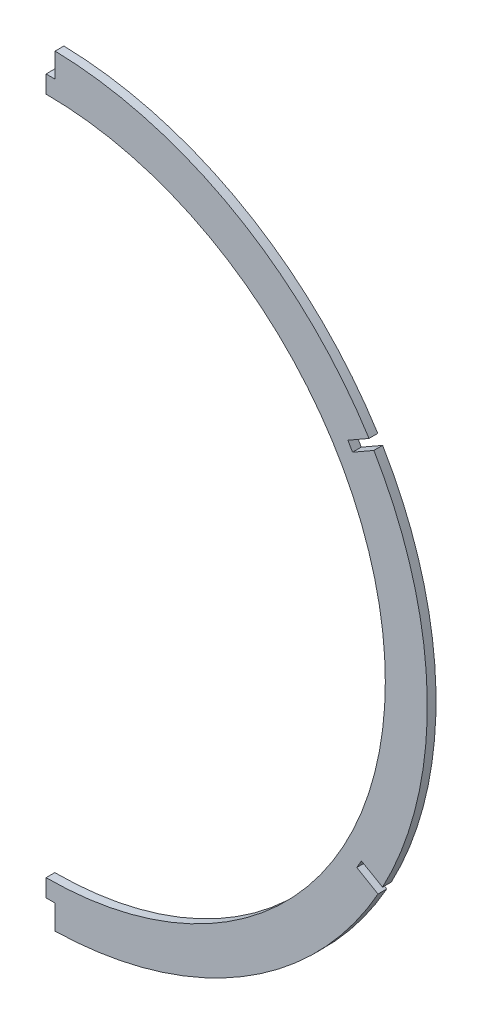
SolidWorks part; units mm, degrees
material "Plywood"
ref_plane "Front Plane" through (0, 0, 0) normal (0, 0, 1) x (1, 0, 0)
ref_plane "Top Plane" through (0, 0, 0) normal (0, 1, 0) x (1, 0, 0)
ref_plane "Right Plane" through (0, 0, 0) normal (1, 0, 0) x (0, 0, -1)
sketch "Sketch1" plane through (0, 0, 0) normal (0, 0, 1) x (1, 0, 0)
  line L0 (0, 32.094) -> (0, -346.2619) construction
  line L1 (0, 0) -> (0, 244.345) construction
  line L2 (0, 0) -> (0, 471.6969) construction
  line L3 (0, 0) -> (-283.5939, 0) construction
  line L4 (-127.2933, -32.5553) -> (-85.9841, -73.8644)
  line L5 (-85.9841, -73.8644) -> (-85.9841, -86.6438)
  line L6 (-85.9841, -73.8644) -> (-54.3993, -105.4493) construction
  arc A0 (-54.3993, -105.4493) -> (-127.2933, -32.5553) centre (0, 21.844) ccw
  arc A2 (-82.075, -89.6305) -> (-54.3993, -105.4493) centre (0, 21.844) ccw construction
  arc A3 (-127.2933, -32.5553) -> (-82.075, -89.6305) centre (0, 21.844) ccw construction
  arc A4 (-85.9841, -86.6438) -> (-54.3993, -105.4493) centre (0, 21.844) ccw
  spline S2 degree 3 poles (-19.218, -1838.2141) (276.9397, -392.4777) (232.9593, 72.7514) (49.9381, 150.9258) (45.7097, 152.4909) (37.1079, 155.2035) (32.7346, 156.3511) (27.1752, 157.5183) (26.0587, 157.7384) (23.8163, 158.1514) (22.6888, 158.3447) (19.306, 158.8811) (17.0511, 159.1813) (10.2867, 159.9126) (1.2693, 160.4377) (-7.745, 160.0789) (-14.5046, 159.4749) (-16.7575, 159.2176) (-20.1367, 158.7464) (-21.263, 158.5751) (-23.5156, 158.2037) (-24.6421, 158.0036) (-30.2426, 156.9366) (-34.6466, 155.8674) (-43.3063, 153.3113) (-47.562, 151.8242) (-55.9254, 148.4331) (-60.0331, 146.529) (-66.0807, 143.3516) (-68.0818, 142.2359) (-72.0044, 139.9197) (-73.9301, 138.7173) (-79.6017, 134.9792) (-86.884, 129.6473) (-93.6143, 123.6295) (-98.4521, 118.8554) (-100.0296, 117.2204) (-102.3424, 114.7015) (-103.1054, 113.8496) (-104.6077, 112.1297) (-105.3467, 111.2623) (-108.9818, 106.8875) (-111.6981, 103.2683) (-116.7574, 95.7975) (-119.1004, 91.9459) (-123.4121, 84.0098) (-125.3809, 79.9253) (-127.6006, 74.6695) (-128.0327, 73.61) (-128.8681, 71.4874) (-129.2719, 70.423) (-130.4422, 67.2205) (-131.1674, 65.0732) (-133.1812, 58.5951) (-135.4347, 49.861) (-136.834, 40.9354) (-137.5569, 34.168) (-137.7434, 31.9) (-137.9397, 28.4793) (-137.9911, 27.3374) (-138.0656, 25.0596) (-138.0887, 23.9223) (-138.135, 18.2442) (-137.9496, 13.7276) (-137.1441, 4.7454) (-136.5239, 0.2797) (-134.8456, -8.6005) (-133.7876, -13.015) (-131.2181, -21.791) (-129.7278, -26.0794) (-126.351, -34.4622) (-124.4643, -38.5569) (-120.2966, -46.5538) (-118.0156, -50.456) (-114.9122, -55.2108) (-114.2789, -56.1556) (-112.9868, -58.0327) (-112.3272, -58.9661) (-110.315, -61.7398) (-108.9333, -63.5482) (-104.6702, -68.8537) (-98.6716, -75.6089) (-92.0553, -81.7381) (-86.8592, -86.0978) (-85.0881, -87.5114) (-82.3719, -89.5716) (-81.4566, -90.2482) (-79.6058, -91.5811) (-78.6696, -92.238) (117.1329, -226.0075) (630.1685, 154.3992) (1500.4507, 1111.3958) knots -1.313799 -1.313799 -1.313799 -1.313799 0.03125 0.03125 0.0625 0.0625 0.09375 0.09375 0.101563 0.101563 0.109375 0.109375 0.125 0.125 0.15625 0.1875 0.1875 0.203125 0.203125 0.210937 0.210937 0.21875 0.21875 0.25 0.25 0.28125 0.28125 0.3125 0.3125 0.328125 0.328125 0.34375 0.34375 0.375 0.40625 0.40625 0.421875 0.421875 0.429687 0.429687 0.4375 0.4375 0.46875 0.46875 0.5 0.5 0.53125 0.53125 0.539062 0.539062 0.546875 0.546875 0.5625 0.5625 0.59375 0.625 0.625 0.640625 0.640625 0.648437 0.648437 0.65625 0.65625 0.6875 0.6875 0.71875 0.71875 0.75 0.75 0.78125 0.78125 0.8125 0.8125 0.84375 0.84375 0.851562 0.851562 0.859375 0.859375 0.875 0.875 0.90625 0.9375 0.9375 0.953125 0.953125 0.960937 0.960937 0.96875 0.96875 2.582348 2.582348 2.582348 2.582348 only from (66.3397, 143.1887) to (-66.0465, -100.0388)
  spline S3 degree 3 poles (66.3397, 143.1887) (62.3323, 145.3909) (58.2494, 147.3758) (49.9381, 150.9258) (45.7097, 152.4909) (37.1079, 155.2035) (32.7346, 156.3511) (27.1752, 157.5183) (26.0587, 157.7384) (23.8163, 158.1514) (22.6888, 158.3447) (19.306, 158.8811) (17.0511, 159.1813) (10.2867, 159.9126) (1.2693, 160.4377) (-7.745, 160.0789) (-14.5046, 159.4749) (-16.7575, 159.2176) (-20.1367, 158.7464) (-21.263, 158.5751) (-23.5156, 158.2037) (-24.6421, 158.0036) (-30.2426, 156.9366) (-34.6466, 155.8674) (-43.3063, 153.3113) (-47.562, 151.8242) (-55.9254, 148.4331) (-60.0331, 146.529) (-66.0807, 143.3516) (-68.0818, 142.2359) (-72.0044, 139.9197) (-73.9301, 138.7173) (-79.6017, 134.9792) (-86.884, 129.6473) (-93.6143, 123.6295) (-98.4521, 118.8554) (-100.0296, 117.2204) (-102.3424, 114.7015) (-103.1054, 113.8496) (-104.6077, 112.1297) (-105.3467, 111.2623) (-108.9818, 106.8875) (-111.6981, 103.2683) (-116.7574, 95.7975) (-119.1004, 91.9459) (-123.4121, 84.0098) (-125.3809, 79.9253) (-127.6006, 74.6695) (-128.0327, 73.61) (-128.8681, 71.4874) (-129.2719, 70.423) (-130.4422, 67.2205) (-131.1674, 65.0732) (-133.1812, 58.5951) (-135.4347, 49.861) (-136.834, 40.9354) (-137.5569, 34.168) (-137.7434, 31.9) (-137.9397, 28.4793) (-137.9911, 27.3374) (-138.0656, 25.0596) (-138.0887, 23.9223) (-138.135, 18.2442) (-137.9496, 13.7276) (-137.1441, 4.7454) (-136.5239, 0.2797) (-134.8456, -8.6005) (-133.7876, -13.015) (-131.2181, -21.791) (-129.7278, -26.0794) (-127.6847, -31.1513) (-127.3213, -32.0275) (-126.9491, -32.8995) knots 0 0 0 0 0.03125 0.03125 0.0625 0.0625 0.09375 0.09375 0.101563 0.101563 0.109375 0.109375 0.125 0.125 0.15625 0.1875 0.1875 0.203125 0.203125 0.210937 0.210937 0.21875 0.21875 0.25 0.25 0.28125 0.28125 0.3125 0.3125 0.328125 0.328125 0.34375 0.34375 0.375 0.40625 0.40625 0.421875 0.421875 0.429687 0.429687 0.4375 0.4375 0.46875 0.46875 0.5 0.5 0.53125 0.53125 0.539062 0.539062 0.546875 0.546875 0.5625 0.5625 0.59375 0.625 0.625 0.640625 0.640625 0.648437 0.648437 0.65625 0.65625 0.6875 0.6875 0.71875 0.71875 0.75 0.75 0.78125 0.78125 0.787815 0.787815 0.787815 0.787815 construction
  point P2 (0, 160.2226)
  point P3 (0, -116.9127)
  point P23 (-85.9841, -73.8644)
  dimension "D1" = 277.1353
  dimension "D2" = 276.86
  dimension "D3" = 21.844
  dimension "D5" = 45
  dimension "D6" = 113.03
  dimension "D4" = 58.42
  dimension "D7" = 45
extrude "Boss-Extrude1" add sketch "Sketch1" along normal mid plane 3.175
sketch "Sketch2" plane through (0, 0, 1.5875) normal (0, 0, 1) x (1, 0, 0)
  line L4 (-114.3729, -23.9231) -> (-70.7441, -67.5518)
  line L5 (-70.7441, -67.5518) -> (-70.7441, -79.0076)
  line L6 (-114.3729, -23.9231) -> (-70.7441, -67.5518)
  line L7 (-70.7441, -67.5518) -> (-70.7441, -79.0076)
  arc A2 (-70.7441, -79.0076) -> (-114.3729, -23.9231) centre (0, 21.844) ccw
  arc A3 (-70.7441, -79.0076) -> (-114.3729, -23.9231) centre (0, 21.844) ccw
  dimension "D1" = 15.24
extrude "Cut-Extrude1" cut sketch "Sketch2" against normal up to surface (3.175 mm away) up to face at (-27.5361, -9.1994, -1.5875)
fillet "Fillet1" radius 8.89 6 edges at (-127.2933, -32.5553, 0) (-114.3729, -23.9231, 0) (-85.9841, -73.8644, 0) (-85.9841, -86.6438, 0) (-70.7441, -67.5518, 0) (-70.7441, -79.0076, 0)
sketch "Sketch3" plane through (0, 0, 1.5875) normal (0, 0, 1) x (1, 0, 0)
  line L0 (0, 49.992) -> (0, 733.2) construction
  line L1 (0, 49.992) -> (0, 733.2) construction
  line L2 (-136.2041, -28.3557) -> (0, 49.992) construction
  line L3 (136.2041, -28.3557) -> (0, 49.992) construction
  line L4 (-136.2041, -28.3557) -> (0, 49.992) construction
  line L5 (136.2041, -28.3557) -> (0, 49.992) construction
  line L6 (-1.651, 152.6442) -> (-1.651, 160.2642)
  line L7 (1.651, 152.6442) -> (1.651, 160.2642)
  line L8 (-1.651, 152.6442) -> (1.651, 152.6442)
  line L9 (119.8454, -45.9681) -> (106.751, -38.3801)
  line L10 (121.4405, -43.2127) -> (108.3453, -35.6242)
  line L11 (-126.0584, -33.7901) -> (-88.588, -71.2606)
  line L12 (-85.9841, -77.5468) -> (-85.9841, -82.2574)
  line L13 (-126.0584, -33.7901) -> (-88.588, -71.2606) construction
  line L14 (-85.9841, -77.5468) -> (-85.9841, -82.2574) construction
  line L18 (121.4405, -43.2127) -> (108.3453, -35.6242)
  line L30 (-123.167, -47.8929) -> (-104.8699, -37.29)
  line L35 (119.8454, -45.9681) -> (106.751, -38.3801)
  line L36 (-109.2131, -37.6397) -> (-109.8693, -36.5073)
  line L47 (108.5244, -35.721) -> (120.1169, -46.1175) construction
  line L48 (114.3206, -40.9193) -> (126.5619, -48.0121) construction
  line L49 (113.8577, -42.5592) -> (122.0137, -47.2849)
  line L50 (115.5132, -39.7021) -> (123.6691, -44.4278)
  line L51 (113.8577, -42.5592) -> (115.5132, -39.7021)
  line L52 (122.0137, -47.2849) -> (123.6691, -44.4278)
  line L58 (-124.7703, -45.1423) -> (-109.8693, -36.5073)
  line L59 (-124.7703, -45.1423) -> (-123.167, -47.8929)
  line L67 (-105.8098, -35.6675) -> (-109.2131, -37.6397)
  line L71 (-124.7703, -45.1423) -> (-123.167, -47.8929) construction
  line L72 (-124.7703, -45.1423) -> (-109.8693, -36.5073) construction
  line L73 (-123.167, -47.8929) -> (-104.8699, -37.29) construction
  line L74 (-123.167, -47.8929) -> (-107.9499, -35.3951) construction
  line L75 (-115.5584, -41.644) -> (-110.9064, -38.9482) construction
  line L76 (-119.3826, -41.9518) -> (-112.6266, -38.0369)
  line L77 (-117.727, -44.8088) -> (-110.971, -40.8938)
  line L78 (-119.3826, -41.9518) -> (-117.727, -44.8088)
  line L79 (-112.6266, -38.0369) -> (-110.971, -40.8938)
  line L82 (-105.8098, -35.6675) -> (-109.2131, -37.6397) construction
  line L83 (-109.2131, -37.6397) -> (-109.8693, -36.5073) construction
  arc A0 (-54.3993, -105.4493) -> (-127.2933, -32.5553) centre (0, 21.844) ccw construction
  arc A2 (-1.651, 160.2642) -> (-130.2816, -24.9489) centre (0, 21.844) ccw construction
  arc A3 (-130.2816, -24.9489) -> (-127.2933, -32.5553) centre (0, 21.844) ccw construction
  arc A4 (-1.651, 160.2642) -> (-130.2816, -24.9489) centre (0, 21.844) ccw construction
  arc A5 (-130.2816, -24.9489) -> (-127.9919, -30.8906) centre (0, 21.844) ccw construction
  arc A6 (-82.3849, -89.4016) -> (-127.9919, -30.8906) centre (0, 21.844) ccw
  arc A7 (-127.9919, -30.8906) -> (-126.0584, -33.7901) centre (-119.7722, -27.504) ccw
  arc A8 (-85.9841, -77.5468) -> (-88.588, -71.2606) centre (-94.8741, -77.5468) ccw
  arc A9 (-85.9841, -82.2574) -> (-82.3849, -89.4016) centre (-77.0941, -82.2574) ccw
  arc A11 (-127.9919, -30.8906) -> (-126.0584, -33.7901) centre (-119.7722, -27.504) ccw construction
  arc A12 (-85.9841, -77.5468) -> (-88.588, -71.2606) centre (-94.8741, -77.5468) ccw construction
  arc A13 (-85.9841, -82.2574) -> (-82.3849, -89.4016) centre (-77.0941, -82.2574) ccw construction
  arc A14 (130.2816, -24.9489) -> (1.651, 160.2642) centre (0, 21.844) ccw construction
  arc A15 (1.651, 160.2642) -> (-1.651, 160.2642) centre (0, 21.844) ccw
  arc A16 (130.2816, -24.9489) -> (1.651, 160.2642) centre (0, 21.844) ccw construction
  arc A17 (1.651, 160.2642) -> (-1.651, 160.2642) centre (0, 21.844) ccw
  spline S0 degree 3 poles (106.751, -38.3801) (107.2824, -37.4615) (107.8139, -36.5429) (108.3453, -35.6242) knots 0 0 0 0 1 1 1 1 weights 1 1 1 1
  spline S1 degree 3 poles (119.8454, -45.9681) (120.3771, -45.0496) (120.9088, -44.1312) (121.4405, -43.2127) knots 0 0 0 0 1 1 1 1 weights 1 1 1 1
  spline S2 degree 3 poles (-885.9995, -1769.7517) (-211.5636, -622.9991) (457.4593, 532.6423) (1115.3786, 1687.3419) knots -628.025775 -628.025775 -628.025775 -628.025775 629.321979 629.321979 629.321979 629.321979 weights 1.00213 0.999289 0.99929 1.002132 only from (119.8454, -45.9681) to (121.4405, -43.2127)
  spline S3 degree 3 poles (-1102.3122, 1695.2927) (-441.4553, 540.1286) (227.4994, -614.6331) (901.0143, -1762.8764) knots -1066.678373 -1066.678373 -1066.678373 -1066.678373 1067.563855 1067.563855 1067.563855 1067.563855 weights 1.001327 0.999558 0.999558 1.001327 only from (-105.8098, -35.6675) to (-104.8699, -37.29)
  spline S4 degree 3 poles (-105.8098, -35.6675) (-105.4965, -36.2084) (-105.1832, -36.7492) (-104.8699, -37.29) knots 0 0 0 0 1 1 1 1 weights 1 1 1 1 construction
  spline S6 degree 3 poles (-898.4881, -1762.9922) (-224.3422, -615.0331) (444.2887, 540.7283) (1102.2727, 1695.4213) knots -627.922306 -627.922306 -627.922306 -627.922306 629.42597 629.42597 629.42597 629.42597 weights 1.001921 0.999359 0.99936 1.001924 only from (106.751, -38.3801) to (108.3453, -35.6242)
  point P49 (-116.0256, -43.8229)
  point P50 (120.451, -46.3794)
  arc M19 (-82.3849, -89.4016) -> (-127.9919, -30.8906) centre (0, 21.844) ccw
  line M21 (-126.0584, -33.7901) -> (-88.588, -71.2606)
  dimension "D1" = 3.302
  dimension "D2" = 7.62
  dimension "D4" = 3.302
  dimension "D5" = 7.62
  dimension "D6" = 3.302
  dimension "D7" = 5.842
  dimension "D3" = 0
extrude "Cut-Extrude2" [suppressed] cut sketch "Sketch3" against normal through all contours L79 L76 L77 M21 | L6 L8 L7 M19 | L51 L49 L50 M19
sketch "Sketch4" plane through (0, 0, 0) normal (1, 0, 0) x (0, 0, -1)
  line L1 (-96.2805, 232.7957) -> (122.2438, 232.7957)
  line L2 (-96.2805, 232.7957) -> (-96.2805, -207.8589)
  line L3 (-96.2805, -207.8589) -> (122.2438, -207.8589)
  line L4 (122.2438, 232.7957) -> (122.2438, -207.8589)
extrude "Cut-Extrude3" cut sketch "Sketch4" against normal through all
sketch "Sketch5" plane through (0, 0, -1.5875) normal (0, 0, -1) x (-1, 0, 0)
  line L0 (0, 0) -> (0, 145.034) construction
  line L1 (0, 145.034) -> (0, 151.384) construction
  line L2 (104.929, 86.3862) -> (0, 26.2525) construction
  line L3 (-3.302, 151.384) -> (3.302, 151.384)
  line L4 (0, 151.384) -> (0, 164.084)
  line L5 (-3.302, 164.084) -> (3.302, 164.084)
  line L6 (3.302, 151.384) -> (3.302, 164.084)
  line L7 (104.929, 86.3862) -> (110.4384, 89.5435) construction
  line L8 (109.5985, 91.009) -> (111.2782, 88.078)
  line L9 (109.5985, 91.009) -> (120.6173, 97.3238)
  line L10 (111.2782, 88.078) -> (122.297, 94.3928)
  line L11 (120.6173, 97.3238) -> (122.297, 94.3928)
  line L12 (108.1767, -37.0931) -> (0, 25.5937) construction
  line L13 (108.1767, -37.0931) -> (113.6709, -40.2769) construction
  line L14 (112.824, -41.7383) -> (114.5178, -38.8154)
  line L15 (112.824, -41.7383) -> (123.8123, -48.1059)
  line L16 (114.5178, -38.8154) -> (125.5061, -45.183)
  line L17 (123.8123, -48.1059) -> (125.5061, -45.183)
  line L18 (0, 0) -> (0, -101.346) construction
  line L19 (0, -101.346) -> (0, -107.696) construction
  line L20 (-3.302, -107.696) -> (3.302, -107.696)
  line L21 (0, -107.696) -> (0, -120.396)
  line L22 (-3.302, -120.396) -> (3.302, -120.396)
  line L23 (3.302, -107.696) -> (3.302, -120.396)
  line L24 (-108.1767, -37.0931) -> (-113.6709, -40.2769) construction
  line L25 (-108.1767, -37.0931) -> (0, 25.5937) construction
  line L26 (-104.929, 86.3862) -> (-110.4384, 89.5435) construction
  line L27 (-104.929, 86.3862) -> (0, 26.2525) construction
  line L28 (-3.302, -107.696) -> (-3.302, -120.396)
  line L29 (-123.8123, -48.1059) -> (-125.5061, -45.183)
  line L30 (-114.5178, -38.8154) -> (-125.5061, -45.183)
  line L31 (-112.824, -41.7383) -> (-123.8123, -48.1059)
  line L32 (-112.824, -41.7383) -> (-114.5178, -38.8154)
  line L33 (-120.6173, 97.3238) -> (-122.297, 94.3928)
  line L34 (-111.2782, 88.078) -> (-122.297, 94.3928)
  line L35 (-109.5985, 91.009) -> (-120.6173, 97.3238)
  line L36 (-109.5985, 91.009) -> (-111.2782, 88.078)
  line L37 (-3.302, 151.384) -> (-3.302, 164.084)
  point P2 (110.4384, 89.5435)
  point P12 (113.6709, -40.2769)
  arc M20 (0, 160.274) -> (0, -116.586) centre (0, 21.844) ccw
  line M21 (0, -116.586) -> (0, -101.346)
  line M23 (0, 145.034) -> (0, 160.274)
  dimension "D1" = 59.908
  dimension "D2" = 60.183
  dimension "D3" = 145.034
  dimension "D4" = 3.302
  dimension "D5" = 12.7
  dimension "D6" = 6.35
  dimension "D7" = 120.9386
  dimension "D8" = 6.35
  dimension "D9" = 125.0273
  dimension "D10" = 6.35
  dimension "D11" = 3.3782
  dimension "D12" = 12.7
  dimension "D13" = 26.2525
  dimension "D14" = 25.5937
  dimension "D15" = 6.35
  dimension "D16" = 101.346
  dimension "D17" = 3.302
  dimension "D18" = 12.7
  dimension "D19" = 12.7
  dimension "D20" = 3.3782
extrude "Cut-Extrude4" cut sketch "Sketch5" against normal through all contours L31 L32 L30 M20 | L36 L35 L34 M20 | L37 L3 M23 M20 | L20 L28 M20 M21
equation "\"a\"= 0.06"
equation "\"slotwidth\"=0.13"
equation "\"slotheight\"=0.3"
